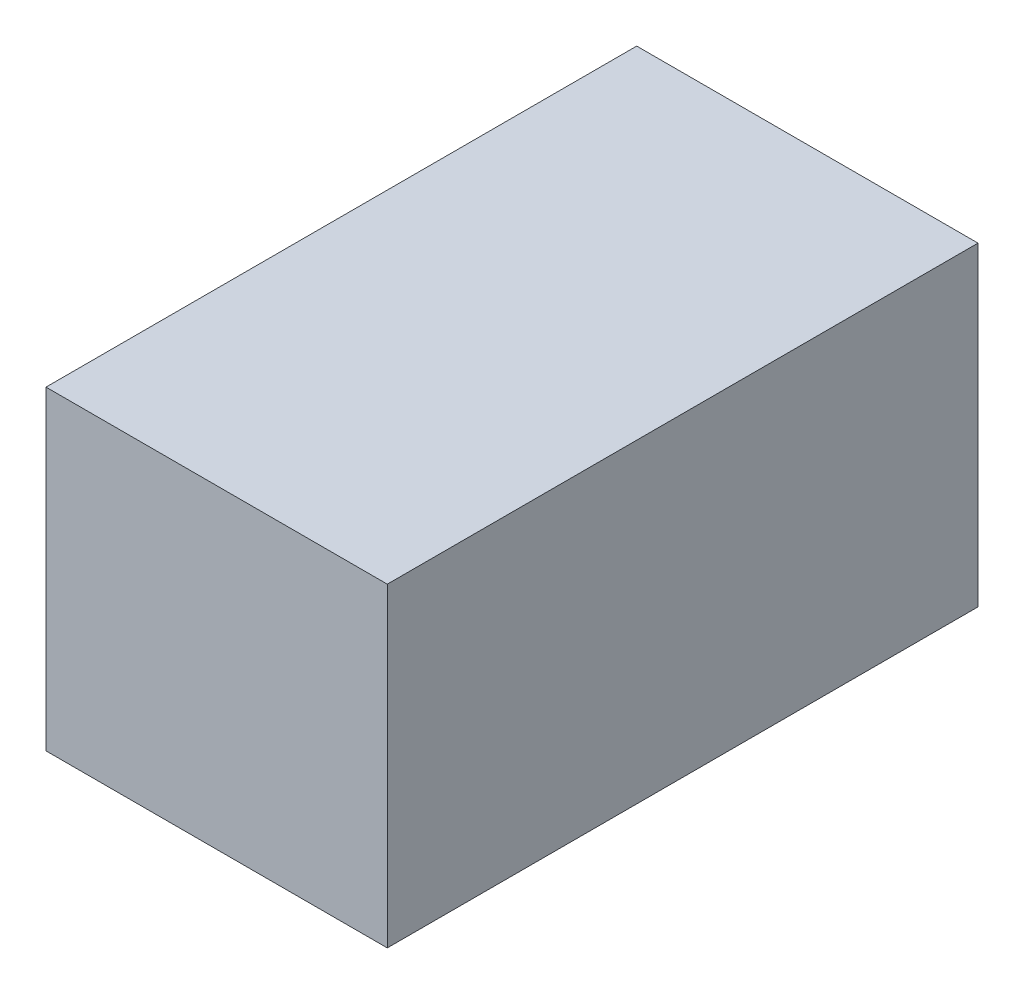
SolidWorks part; units mm, degrees
ref_plane "Front Plane" through (0, 0, 0) normal (0, 0, 1) x (1, 0, 0)
ref_plane "Top Plane" through (0, 0, 0) normal (0, 1, 0) x (1, 0, 0)
ref_plane "Right Plane" through (0, 0, 0) normal (1, 0, 0) x (0, 0, -1)
sketch "Sketch2" plane through (0, 0, 0) normal (0, 1, 0) x (1, 0, 0)
  line L1 (-13, 22.5) -> (13, 22.5)
  line L2 (-13, 22.5) -> (-13, -22.5)
  line L3 (-13, -22.5) -> (13, -22.5)
  line L4 (13, 22.5) -> (13, -22.5)
  line L5 (-13, 22.5) -> (13, -22.5) construction
  line L6 (-13, -22.5) -> (13, 22.5) construction
  point P0 (0, 0)
  dimension "D1" = 45
  dimension "D2" = 26
extrude "Boss-Extrude1" add sketch "Sketch2" along normal mid plane 24
